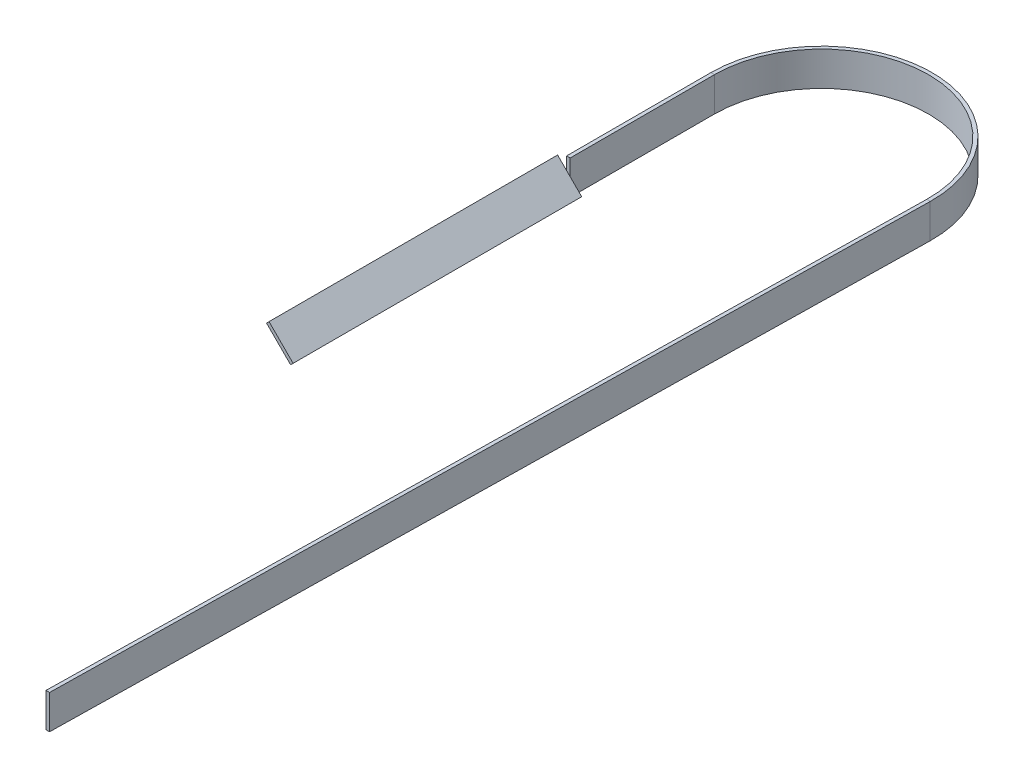
SolidWorks part; units mm, degrees
ref_plane "Front Plane" through (0, 0, 0) normal (0, 0, 1) x (1, 0, 0)
ref_plane "Top Plane" through (0, 0, 0) normal (0, 1, 0) x (1, 0, 0)
ref_plane "Right Plane" through (0, 0, 0) normal (1, 0, 0) x (0, 0, -1)
sketch "Sketch1" plane through (0, 0, 0) normal (0, 1, 0) x (1, 0, 0)
  line L0 (-18.8468, -25.4) -> (-18.8468, 0)
  line L1 (16.1842, -152.7057) -> (18.8439, -0.3289)
  arc A0 (-18.8468, 0) -> (18.8439, -0.3289) centre (0, 0) cw
  dimension "D1" = 18.8468
  dimension "D2" = 1
  dimension "D3" = 25.4
  dimension "D4" = 152.4
ref_plane "Plane1" through (-18.8468, 0, 25.4) normal (0, 0, -1) x (-1, 0, 0)
sketch "Sketch2" plane through (-18.8468, 0, 25.4) normal (0, 0, -1) x (-1, 0, 0)
  line L1 (0, 0) -> (0.63, 0)
  line L2 (0, 0) -> (0, -6)
  line L3 (0, -6) -> (0.63, -6)
  line L4 (0.63, 0) -> (0.63, -6)
  dimension "D1" = 0.63
  dimension "D2" = 6
sweep "Sweep1" add profiles "Sketch2" path "Sketch1"
sketch "Sketch3" plane through (0, 0, 25.4) normal (0, 0, 1) x (1, 0, 0)
  line L0 (-21.0604, -0.6559) -> (-16.8177, -4.8986)
  line L1 (-21.0604, -0.6559) -> (-21.5059, -1.1014)
  line L2 (-16.8177, -4.8986) -> (-17.2632, -5.3441)
  line L3 (-21.5059, -1.1014) -> (-17.2632, -5.3441)
  line L4 (-21.0604, -0.6559) -> (-17.2632, -5.3441) construction
  line L5 (-16.8177, -4.8986) -> (-21.5059, -1.1014) construction
  line L6 (-19.4768, 0) -> (-18.8468, 0) construction
  line L7 (-18.8468, 0) -> (-18.8468, -6) construction
  line L8 (-19.4768, 0) -> (-18.8468, -6) construction
  line L9 (-19.4768, -6) -> (-19.4768, 0) construction
  point P1 (-19.1618, -3)
  point P13 (-19.1618, -3)
  dimension "D1" = 45
extrude "Boss-Extrude1" add sketch "Sketch3" along normal blind 50.8
equation "\"D1@Sketch2\"=1.38mm-.75mm"
